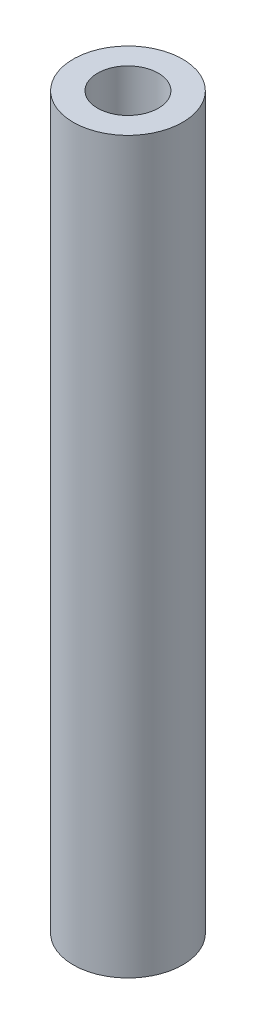
SolidWorks part; units mm, degrees
material "1060 Alloy"
ref_plane "Front Plane" through (0, 0, 0) normal (0, 0, 1) x (1, 0, 0)
ref_plane "Top Plane" through (0, 0, 0) normal (0, 1, 0) x (1, 0, 0)
ref_plane "Right Plane" through (0, 0, 0) normal (1, 0, 0) x (0, 0, -1)
sketch "Sketch1" plane through (0, 0, 0) normal (0, 1, 0) x (1, 0, 0)
  circle A0 centre (1.4079, 0) radius 1.5875
  circle A1 centre (1.4079, 0) radius 2.8575
  dimension "D1" = 1.27
extrude "Boss-Extrude1" add sketch "Sketch1" along normal blind 38.1
